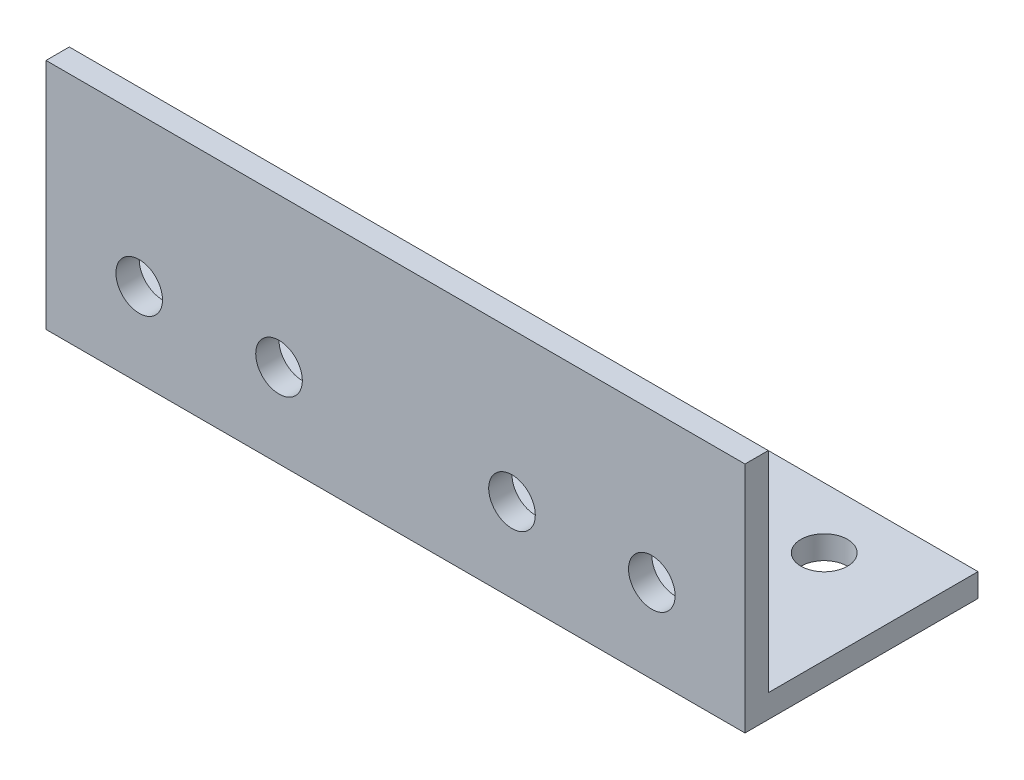
SolidWorks part; units mm, degrees
ref_plane "Спереди" through (0, 0, 0) normal (0, 0, 1) x (1, 0, 0)
ref_plane "Сверху" through (0, 0, 0) normal (0, 1, 0) x (1, 0, 0)
ref_plane "Справа" through (0, 0, 0) normal (1, 0, 0) x (0, 0, -1)
sketch "Эскиз1" plane through (0, 0, 0) normal (1, 0, 0) x (0, 0, -1)
  line L0 (0, 0) -> (0, 50)
  line L1 (0, 0) -> (50, 0)
extrude "Вытянуть-Тонкостенный1" add sketch "Эскиз1" along normal blind 150 thin
sketch "Эскиз2" plane through (0, 0, 0) normal (0, -1, 0) x (1, 0, 0)
  line L0 (75, -58.7293) -> (75, -21.2393) construction
  circle A0 centre (130, -37) radius 5
  circle A1 centre (100, -37) radius 5
  circle A2 centre (50, -37) radius 5
  circle A3 centre (20, -37) radius 5
  dimension "D1" = 2
extrude "Вырез-Вытянуть1" cut sketch "Эскиз2" against normal through all
sketch "Эскиз3" plane through (0, 0, 0) normal (0, 0, 1) x (1, 0, 0)
  line L0 (75, 50) -> (75, 0) construction
  line L1 (150, 50) -> (0, 50) construction
  circle A0 centre (130, 18) radius 5
  circle A1 centre (100, 18) radius 5
  circle A2 centre (50, 18) radius 5
  circle A3 centre (20, 18) radius 5
  dimension "D1" = 2
extrude "Вырез-Вытянуть3" cut sketch "Эскиз3" against normal through all
